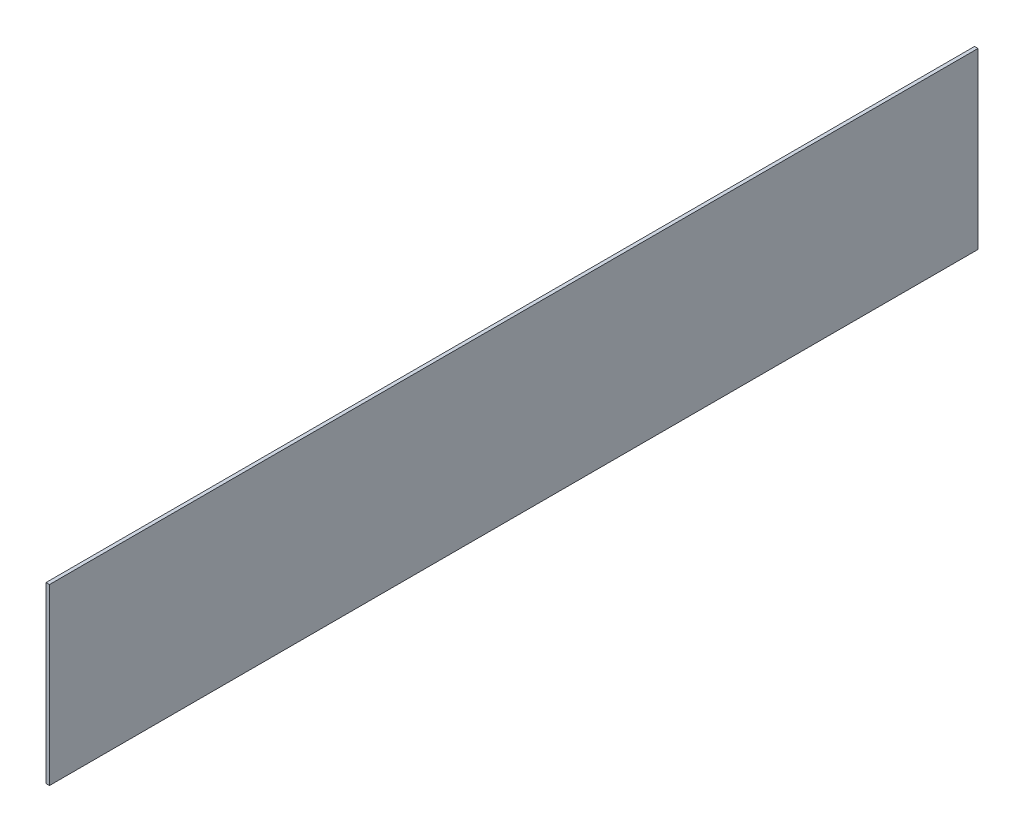
SolidWorks part; units mm, degrees
ref_plane "Front Plane" through (0, 0, 0) normal (0, 0, 1) x (1, 0, 0)
ref_plane "Top Plane" through (0, 0, 0) normal (0, 1, 0) x (1, 0, 0)
ref_plane "Right Plane" through (0, 0, 0) normal (1, 0, 0) x (0, 0, -1)
sketch "Sketch1" plane through (0, 0, 0) normal (1, 0, 0) x (0, 0, -1)
  line L1 (-400, 75) -> (400, 75)
  line L2 (-400, 75) -> (-400, -75)
  line L3 (-400, -75) -> (400, -75)
  line L4 (400, 75) -> (400, -75)
  line L5 (-400, 75) -> (400, -75) construction
  line L6 (-400, -75) -> (400, 75) construction
  point P0 (0, 0)
  dimension "D1" = 150
  dimension "D2" = 800
extrude "Boss-Extrude1" add sketch "Sketch1" along normal blind 3
